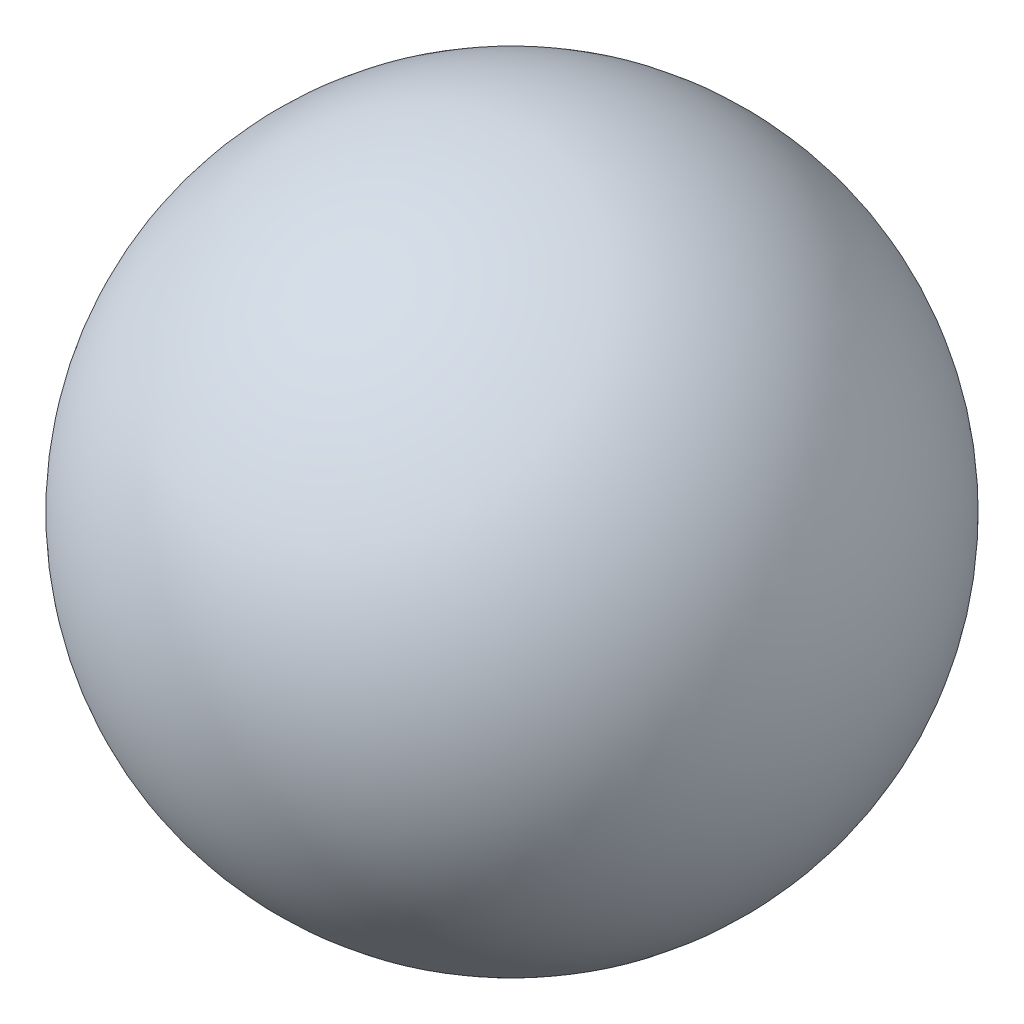
SolidWorks part; units mm, degrees
ref_plane "Vorne" through (0, 0, 0) normal (0, 0, 1) x (1, 0, 0)
ref_plane "Oben" through (0, 0, 0) normal (0, 1, 0) x (1, 0, 0)
ref_plane "Rechts" through (0, 0, 0) normal (1, 0, 0) x (0, 0, -1)
sketch "Skizze2" plane through (0, 0, 0) normal (1, 0, 0) x (0, 0, -1)
  line L0 (0, 23.3761) -> (0, -22.0403) construction
  line L1 (0, 6) -> (0, -6)
  arc A0 (0, -6) -> (0, 6) centre (0, 0) ccw
  dimension "D1" = 12
revolve "Kugel" add sketch "Skizze2" angle 360 about L0
sketch "Skizze3" plane through (0, 0, 0) normal (1, 0, 0) x (0, 0, -1)
  line L0 (0, 3.7991) -> (0, -4.0478) construction
  line L1 (0, 23.3761) -> (0, -22.0403) construction
  circle A0 centre (0, 0) radius 1.5
  circle A1 centre (0, 0) radius 2.5 construction
  circle A2 centre (0, 2.5) radius 0.5
  dimension "D1" = 3
  dimension "D2" = 5
  dimension "D3" = 1
extrude "Achse 1" cut sketch "Skizze3" against normal mid plane 10
sketch "Skizze4" plane through (0, 0, 0) normal (0, 1, 0) x (1, 0, 0)
  line L0 (0, 4.3187) -> (0, -4.8905) construction
  circle A0 centre (0, 0) radius 1.5
  circle A1 centre (0, 0) radius 2.5 construction
  circle A3 centre (0, 2.5) radius 0.5
  dimension "D1" = 3
  dimension "D2" = 5
  dimension "D4" = 1
extrude "Achse 2" cut sketch "Skizze4" against normal mid plane 10
